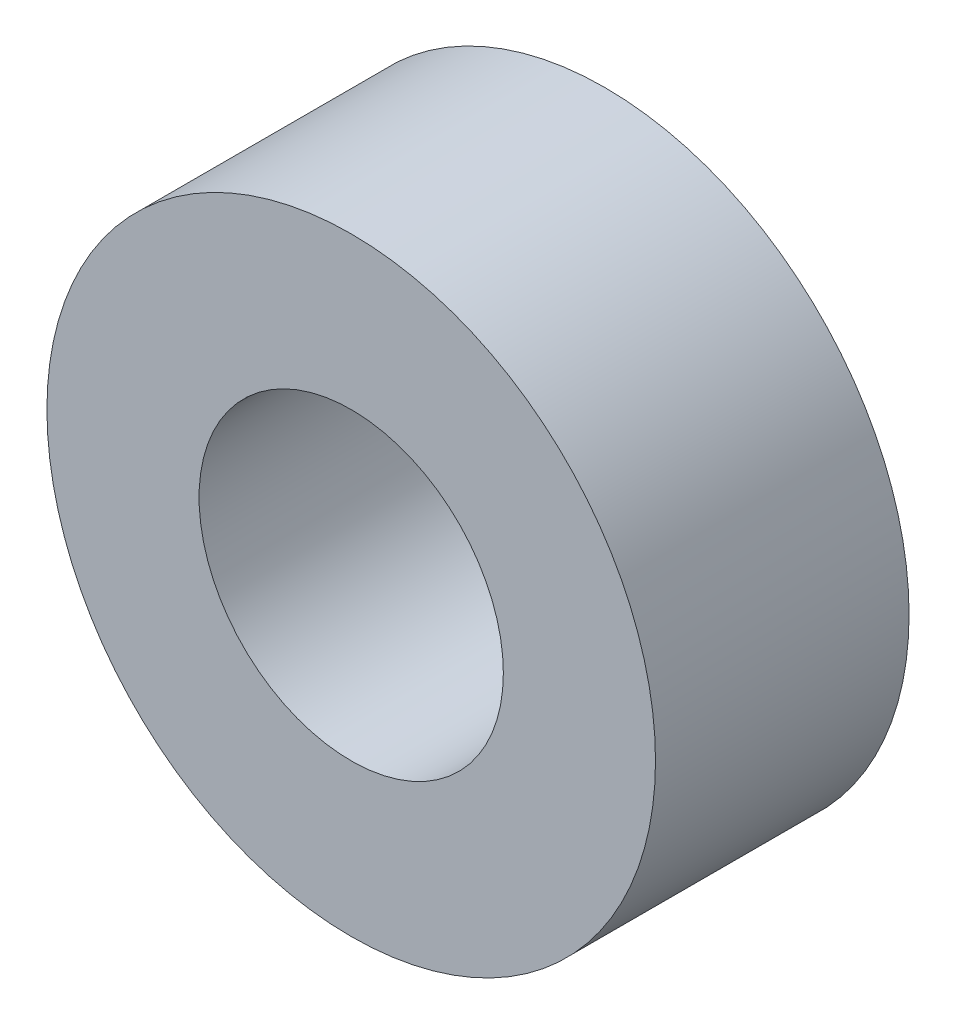
SolidWorks part; units mm, degrees
ref_plane "정면" through (0, 0, 0) normal (0, 0, 1) x (1, 0, 0)
ref_plane "윗면" through (0, 0, 0) normal (0, 1, 0) x (1, 0, 0)
ref_plane "우측면" through (0, 0, 0) normal (1, 0, 0) x (0, 0, -1)
sketch "스케치1" plane through (0, 0, 0) normal (0, 0, 1) x (1, 0, 0)
  circle A0 centre (0, 0) radius 3
  circle A1 centre (0, 0) radius 1.5
  dimension "D1" = 6
  dimension "D2" = 3
extrude "보스-돌출1" add sketch "스케치1" along normal blind 2.5
